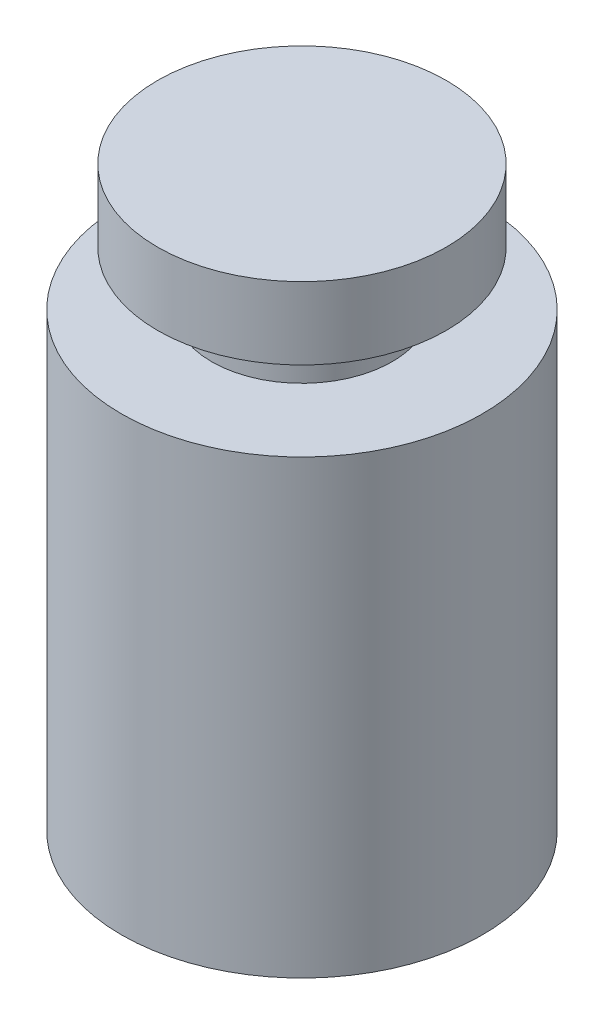
SolidWorks part; units mm, degrees
ref_plane "Piano frontale" through (0, 0, 0) normal (0, 0, 1) x (1, 0, 0)
ref_plane "Piano superiore" through (0, 0, 0) normal (0, 1, 0) x (1, 0, 0)
ref_plane "Piano destro" through (0, 0, 0) normal (1, 0, 0) x (0, 0, -1)
sketch "Schizzo1" plane through (0, 0, 0) normal (0, 0, 1) x (1, 0, 0)
  line L0 (0, 0) -> (-10, 0)
  line L1 (-10, 0) -> (-10, 25)
  line L2 (-10, 25) -> (-5, 25)
  line L3 (-5, 25) -> (-5, 28)
  line L4 (-5, 28) -> (-8, 28)
  line L5 (-8, 28) -> (-8, 32)
  line L6 (-8, 32) -> (0, 32)
  line L7 (0, 43.8679) -> (0, -39.717) construction
  line L8 (0, 0) -> (0, 32)
  point P11 (0, 0)
  point P12 (0, 0)
  dimension "D1" = 10
  dimension "D2" = 25
  dimension "D3" = 3
  dimension "D4" = 4
  dimension "D5" = 8
  dimension "D6" = 3
revolve "Rivoluzione1" add sketch "Schizzo1" angle 360 about L7
